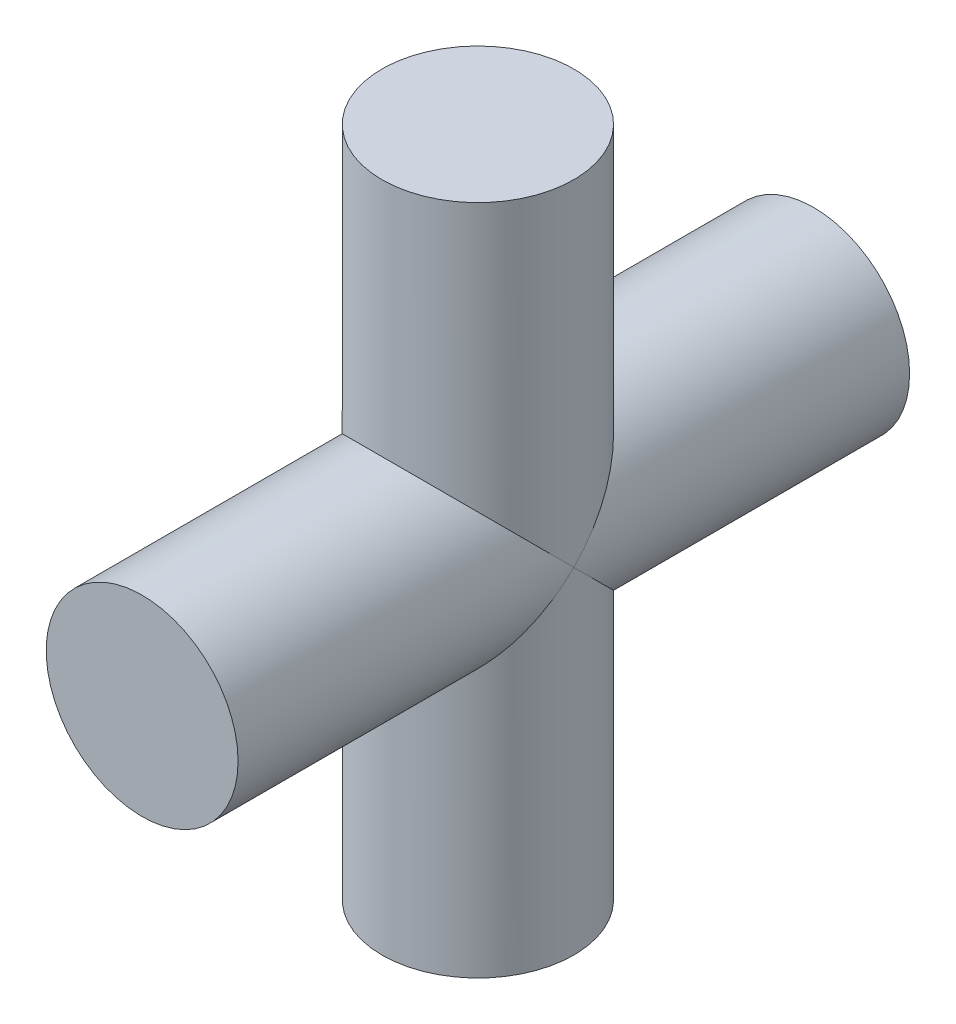
SolidWorks part; units mm, degrees
ref_plane "Front Plane" through (0, 0, 0) normal (0, 0, 1) x (1, 0, 0)
ref_plane "Top Plane" through (0, 0, 0) normal (0, 1, 0) x (1, 0, 0)
ref_plane "Right Plane" through (0, 0, 0) normal (1, 0, 0) x (0, 0, -1)
sketch "Sketch1" plane through (0, 0, 0) normal (0, 0, 1) x (1, 0, 0)
  circle A0 centre (0, 0) radius 3.175
extrude "Boss-Extrude1" add sketch "Sketch1" along normal blind 11.1125 and the other way blind 11.1125
sketch "Sketch2" plane through (0, 0, 0) normal (0, 1, 0) x (1, 0, 0)
  circle A0 centre (0, 0) radius 3.175
extrude "Boss-Extrude2" add sketch "Sketch2" along normal blind 11.1125 and the other way blind 11.1125
